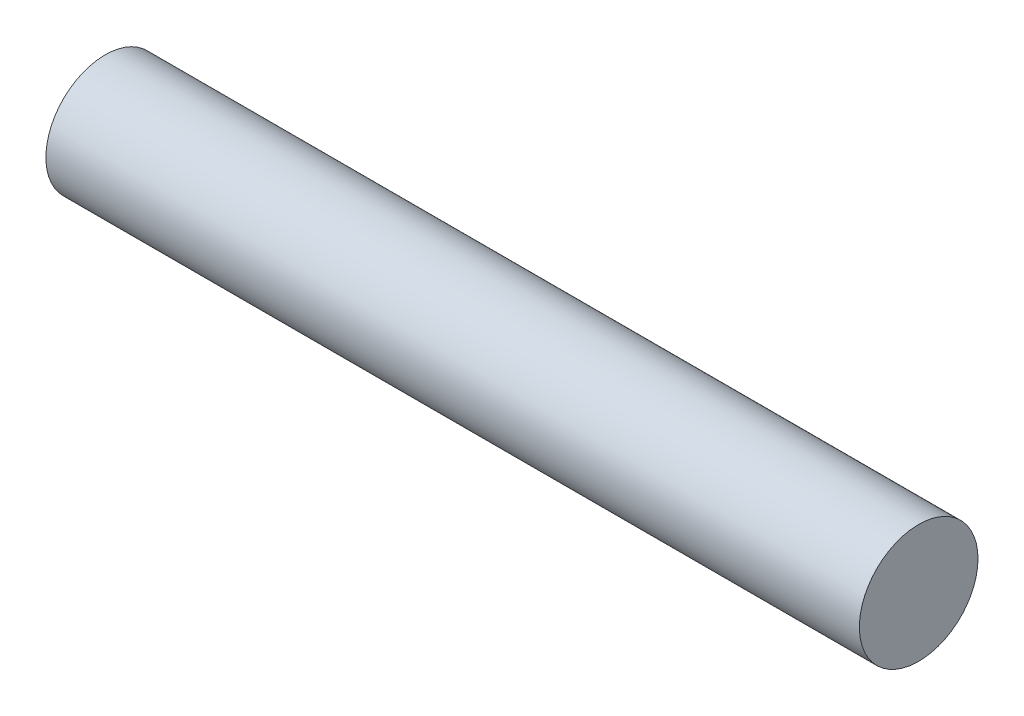
SolidWorks part; units mm, degrees
material "Plain Carbon Steel"
ref_plane "Front Plane" through (0, 0, 0) normal (0, 0, 1) x (1, 0, 0)
ref_plane "Top Plane" through (0, 0, 0) normal (0, 1, 0) x (1, 0, 0)
ref_plane "Right Plane" through (0, 0, 0) normal (1, 0, 0) x (0, 0, -1)
sketch "Sketch1" plane through (0, 0, 0) normal (1, 0, 0) x (0, 0, -1)
  circle A0 centre (0, 0) radius 11.1125
extrude "Boss-Extrude1" add sketch "Sketch1" along normal mid plane 152.4
